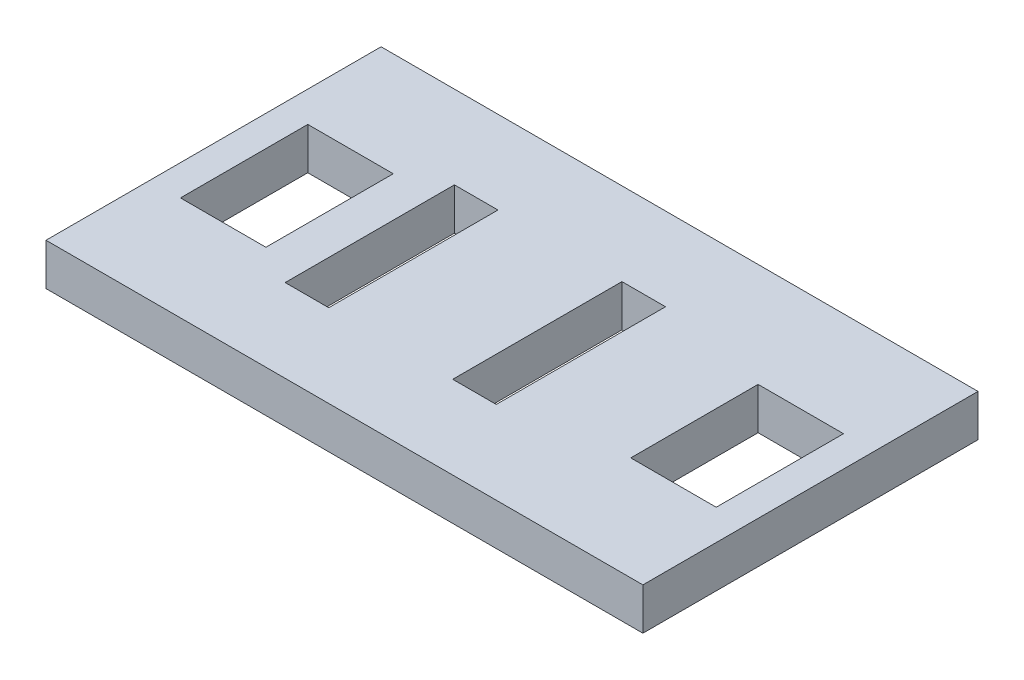
SolidWorks part; units mm, degrees
material "Plain Carbon Steel"
ref_plane "Front Plane" through (0, 0, 0) normal (0, 0, 1) x (1, 0, 0)
ref_plane "Top Plane" through (0, 0, 0) normal (0, 1, 0) x (1, 0, 0)
ref_plane "Right Plane" through (0, 0, 0) normal (1, 0, 0) x (0, 0, -1)
sketch "Sketch1" plane through (0, 0, 0) normal (0, 1, 0) x (1, 0, 0)
  line L0 (0, 25.4) -> (0, 0) construction
  line L1 (-40.4812, -25.4) -> (40.4812, -25.4)
  line L2 (-40.4812, -25.4) -> (-40.4812, 25.4)
  line L3 (-40.4812, 25.4) -> (40.4812, 25.4)
  line L4 (40.4812, -25.4) -> (40.4812, 25.4)
  line L5 (0, 0) -> (40.4812, 0) construction
  dimension "D1" = 40.4812
  dimension "D2" = 25.4
extrude "Boss-Extrude1" add sketch "Sketch1" along normal blind 6.35
sketch "Sketch3" plane through (0, 0, 0) normal (0, -1, 0) x (-1, 0, 0)
  line L0 (14.9542, -12.827) -> (14.9542, 12.827)
  line L1 (-10.3188, 12.7) -> (-3.9688, 12.7)
  line L2 (-10.3188, 12.7) -> (-10.3188, -12.7)
  line L3 (-10.3188, -12.7) -> (-3.9688, -12.7)
  line L4 (-3.9688, 12.7) -> (-3.9688, -12.7)
  line L5 (15.0812, -12.7) -> (21.4312, -12.7)
  line L6 (15.0812, -12.7) -> (15.0812, 12.7)
  line L7 (15.0812, 12.7) -> (21.4312, 12.7)
  line L8 (21.4312, -12.7) -> (21.4312, 12.7)
  line L9 (14.9542, 12.827) -> (21.5582, 12.827)
  line L10 (21.5582, -12.827) -> (21.5582, 12.827)
  line L11 (14.9542, -12.827) -> (21.5582, -12.827)
  line L12 (-3.8418, 12.827) -> (-3.8418, -12.827)
  line L13 (-10.4458, -12.827) -> (-3.8418, -12.827)
  line L14 (-10.4458, 12.827) -> (-10.4458, -12.827)
  line L15 (-10.4458, 12.827) -> (-3.8418, 12.827)
  dimension "D1" = 0.127
extrude "Cut-Extrude1" cut sketch "Sketch3" against normal through all
sketch "Sketch4" plane through (0, 6.35, 0) normal (0, 1, 0) x (1, 0, 0)
  line L1 (-40.4812, 25.4) -> (-45.2437, 25.4)
  line L2 (-40.4812, 25.4) -> (-40.4812, -25.4)
  line L3 (-40.4812, -25.4) -> (-45.2437, -25.4)
  line L4 (-45.2437, 25.4) -> (-45.2437, -25.4)
  line L5 (40.4812, -25.4) -> (45.2438, -25.4)
  line L6 (40.4812, -25.4) -> (40.4812, 25.4)
  line L7 (40.4812, 25.4) -> (45.2438, 25.4)
  line L8 (45.2438, -25.4) -> (45.2438, 25.4)
extrude "Boss-Extrude2" add sketch "Sketch4" against normal up to surface (6.35 mm away) up to face at (7.1438, 0, 0)
sketch "Sketch5" plane through (0, 6.35, 0) normal (0, 1, 0) x (1, 0, 0)
  line L0 (27.6543, -9.652) -> (27.6543, 9.652)
  line L1 (-40.4812, 9.525) -> (-27.7812, 9.525)
  line L2 (-40.4812, 9.525) -> (-40.4812, -9.525)
  line L3 (-40.4812, -9.525) -> (-27.7812, -9.525)
  line L4 (-27.7812, 9.525) -> (-27.7812, -9.525)
  line L5 (27.7813, -9.525) -> (40.4813, -9.525)
  line L6 (27.7813, -9.525) -> (27.7813, 9.525)
  line L7 (27.7813, 9.525) -> (40.4813, 9.525)
  line L8 (40.4813, -9.525) -> (40.4813, 9.525)
  line L9 (27.6543, 9.652) -> (40.6083, 9.652)
  line L10 (40.6083, -9.652) -> (40.6083, 9.652)
  line L11 (27.6543, -9.652) -> (40.6083, -9.652)
  line L12 (-27.6542, 9.652) -> (-27.6542, -9.652)
  line L13 (-40.6082, -9.652) -> (-27.6542, -9.652)
  line L14 (-40.6082, 9.652) -> (-40.6082, -9.652)
  line L15 (-40.6082, 9.652) -> (-27.6542, 9.652)
  dimension "D1" = 0.127
extrude "Cut-Extrude2" cut sketch "Sketch5" against normal through all
